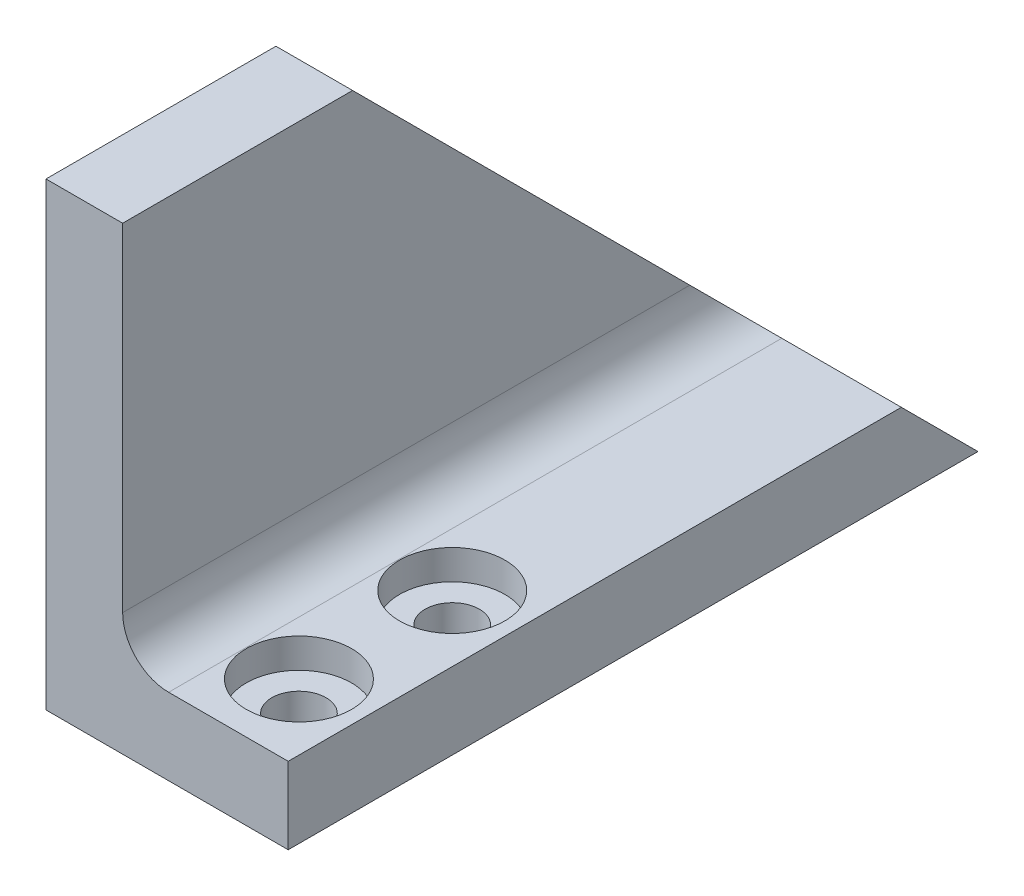
SolidWorks part; units mm, degrees
ref_plane "Front Plane" through (0, 0, 0) normal (0, 0, 1) x (1, 0, 0)
ref_plane "Top Plane" through (0, 0, 0) normal (0, 1, 0) x (1, 0, 0)
ref_plane "Right Plane" through (0, 0, 0) normal (1, 0, 0) x (0, 0, -1)
sketch "Sketch2" plane through (0, 0, 0) normal (0, 1, 0) x (1, 0, 0)
  line L1 (-9.525, -28.575) -> (9.525, -28.575)
  line L2 (-9.525, -28.575) -> (-9.525, 28.575)
  line L3 (-9.525, 28.575) -> (9.525, 28.575)
  line L4 (9.525, -28.575) -> (9.525, 28.575)
  line L5 (-9.525, -28.575) -> (9.525, 28.575) construction
  line L6 (-9.525, 28.575) -> (9.525, -28.575) construction
  point P0 (0, 0)
  dimension "D1" = 57.15
  dimension "D2" = 19.05
extrude "Boss-Extrude2" add sketch "Sketch2" along normal blind 38.1
sketch "Sketch4" plane through (9.525, 0, 0) normal (1, 0, 0) x (0, 0, -1)
  line L0 (28.575, 0) -> (-9.525, 38.1)
  line L1 (-28.575, 0) -> (28.575, 0) construction
  line L2 (-28.575, 38.1) -> (28.575, 38.1) construction
  line L3 (-9.525, 38.1) -> (28.575, 38.1)
  line L4 (28.575, 38.1) -> (28.575, 0)
  dimension "D1" = 45
extrude "Cut-Extrude2" cut sketch "Sketch4" against normal through all
sketch "Sketch7" plane through (0, 0, 28.575) normal (0, 0, 1) x (1, 0, 0)
  line L0 (-9.525, 38.1) -> (-9.525, 0) construction
  line L1 (22.225, 69.85) -> (-3.175, 69.85)
  line L2 (22.225, 69.85) -> (22.225, 6.35)
  line L3 (22.225, 6.35) -> (-3.175, 6.35)
  line L4 (-3.175, 69.85) -> (-3.175, 6.35)
  line L5 (22.225, 69.85) -> (-3.175, 6.35) construction
  line L6 (22.225, 6.35) -> (-3.175, 69.85) construction
  line L7 (-9.525, 0) -> (9.525, 0) construction
  point P0 (9.525, 38.1)
  dimension "D1" = 6.35
  dimension "D2" = 6.35
extrude "Cut-Extrude5" cut sketch "Sketch7" against normal blind 63.5
fillet "Fillet3" radius 3.81 1 edges at (-3.175, 6.35, 3.175)
sketch "Sketch9" plane through (0, 6.35, 0) normal (0, 1, 0) x (1, 0, 0)
  line L0 (5.08, -28.575) -> (5.08, -6.6645) construction
  line L1 (0.635, -28.575) -> (9.525, -28.575) construction
  point P4 (5.08, -22.225)
  point P5 (5.08, -9.525)
  dimension "D1" = 6.35
  dimension "D2" = 12.7
hole_wizard "CBORE for #8 Button Head Cap Screw1" positions "Sketch10" profile "Sketch11" counterbore size "#8" standard "ANSI Inch" end condition through all
sketch "Sketch10" plane through (0, 6.35, 0) normal (0, 1, 0) x (1, 0, 0)
  point P0 (5.08, -22.225)
  point P3 (5.08, -9.525)
sketch "Sketch11" plane through (5.08, 6.35, 22.225) normal (1, 0, 0) x (0, 0, 1)
  line L0 (0, 0) -> (0, 6.35)
  line L1 (0, 6.35) -> (2.2479, 6.35)
  line L3 (2.2479, 6.35) -> (2.2479, 2.4638)
  line L4 (2.2479, 2.4638) -> (4.3663, 2.4638)
  line L5 (4.3663, 2.4638) -> (4.3663, 0)
  line L7 (4.3663, 0) -> (0, 0)
  line L11 (0, -6.35) -> (0, 107.95) construction
  dimension "Thru Hole Dia." = 4.4958
  dimension "Thru Hole Depth" = 6.35
  dimension "C'Bore Dia." = 8.7325
  dimension "C'Bore Depth" = 2.4638
sketch "Sketch12" plane through (9.525, 0, 0) normal (1, 0, 0) x (0, 0, -1)
  line L4 (28.575, 0) -> (22.225, 6.35)
  line L5 (22.225, 6.35) -> (-28.575, 6.35)
  line L6 (-28.575, 6.35) -> (-28.575, 0)
  line L7 (-28.575, 0) -> (28.575, 0)
  line L8 (28.575, 0) -> (22.225, 6.35)
  line L9 (22.225, 6.35) -> (-28.575, 6.35)
  line L10 (-28.575, 6.35) -> (-28.575, 0)
  line L11 (-28.575, 0) -> (28.575, 0)
  dimension "D1" = 0
extrude "Boss-Extrude3" add sketch "Sketch12" along normal blind 1.016
